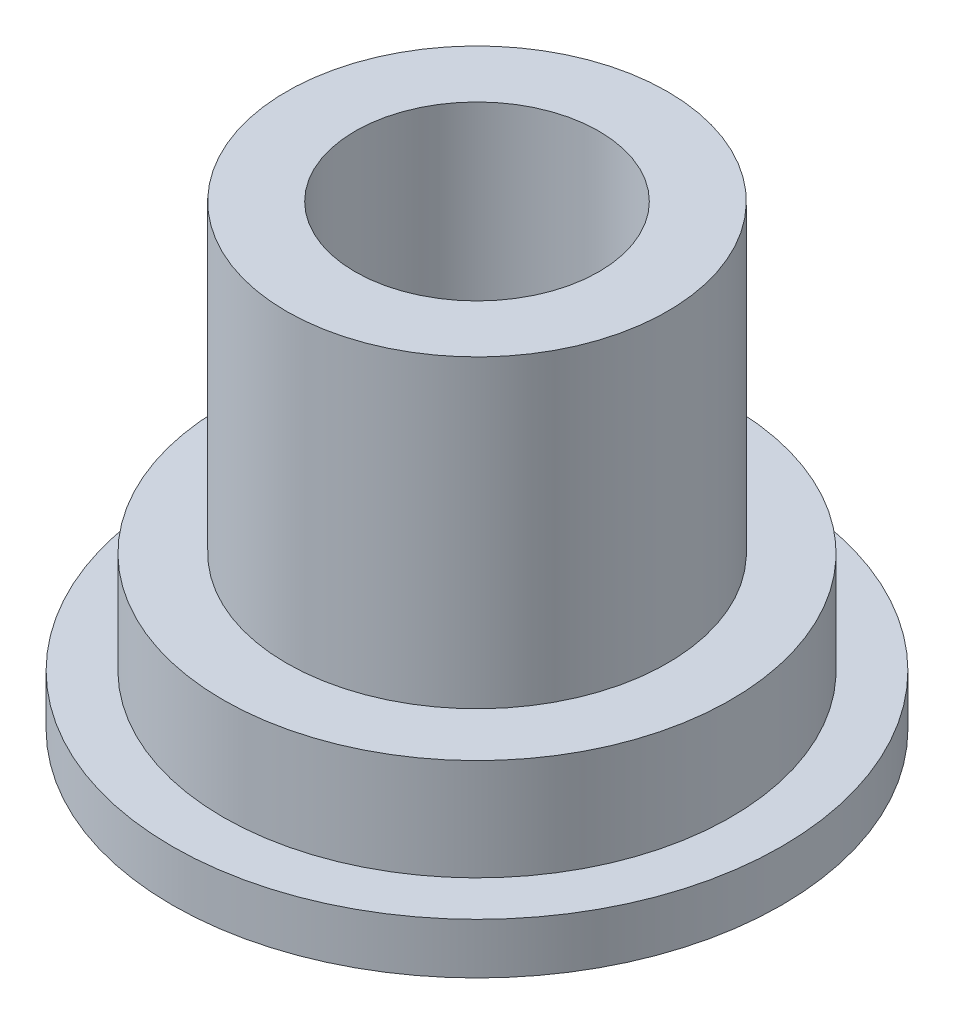
SolidWorks part; units mm, degrees
ref_plane "Front Plane" through (0, 0, 0) normal (0, 0, 1) x (1, 0, 0)
ref_plane "Top Plane" through (0, 0, 0) normal (0, 1, 0) x (1, 0, 0)
ref_plane "Right Plane" through (0, 0, 0) normal (1, 0, 0) x (0, 0, -1)
sketch "Sketch1" plane through (0, 0, 0) normal (0, 1, 0) x (1, 0, 0)
  circle A0 centre (0, 0) radius 6.35
extrude "Boss-Extrude1" add sketch "Sketch1" along normal blind 2.54
sketch "Sketch2" plane through (0, 2.54, 0) normal (0, 1, 0) x (1, 0, 0)
  circle A0 centre (0, 0) radius 4.7625
extrude "Boss-Extrude2" add sketch "Sketch2" along normal blind 7.62
sketch "Sketch3" plane through (0, 10.16, 0) normal (0, 1, 0) x (1, 0, 0)
  circle A0 centre (0, 0) radius 3.048
extrude "Cut-Extrude1" cut sketch "Sketch3" against normal blind 7.62
sketch "Sketch6" plane through (0, 0, 0) normal (0, -1, 0) x (1, 0, 0)
  circle A0 centre (0, 0) radius 7.62
extrude "Boss-Extrude3" add sketch "Sketch6" along normal blind 1.27
sketch "Sketch4" plane through (0, 2.54, 0) normal (0, 1, 0) x (1, 0, 0)
  circle A0 centre (0, -1.27) radius 0.762
  point P0 (0, 0)
  point P1 (0, -1.27)
  dimension "D1" = 1.27
sketch "Sketch5" plane through (0, 2.54, 0) normal (0, 1, 0) x (1, 0, 0)
  circle A0 centre (0, 1.27) radius 0.762
  point P0 (0, 1.27)
extrude "Cut-Extrude2" cut sketch "Sketch4" against normal through all and the other way through all
extrude "Cut-Extrude3" cut sketch "Sketch5" against normal through all
